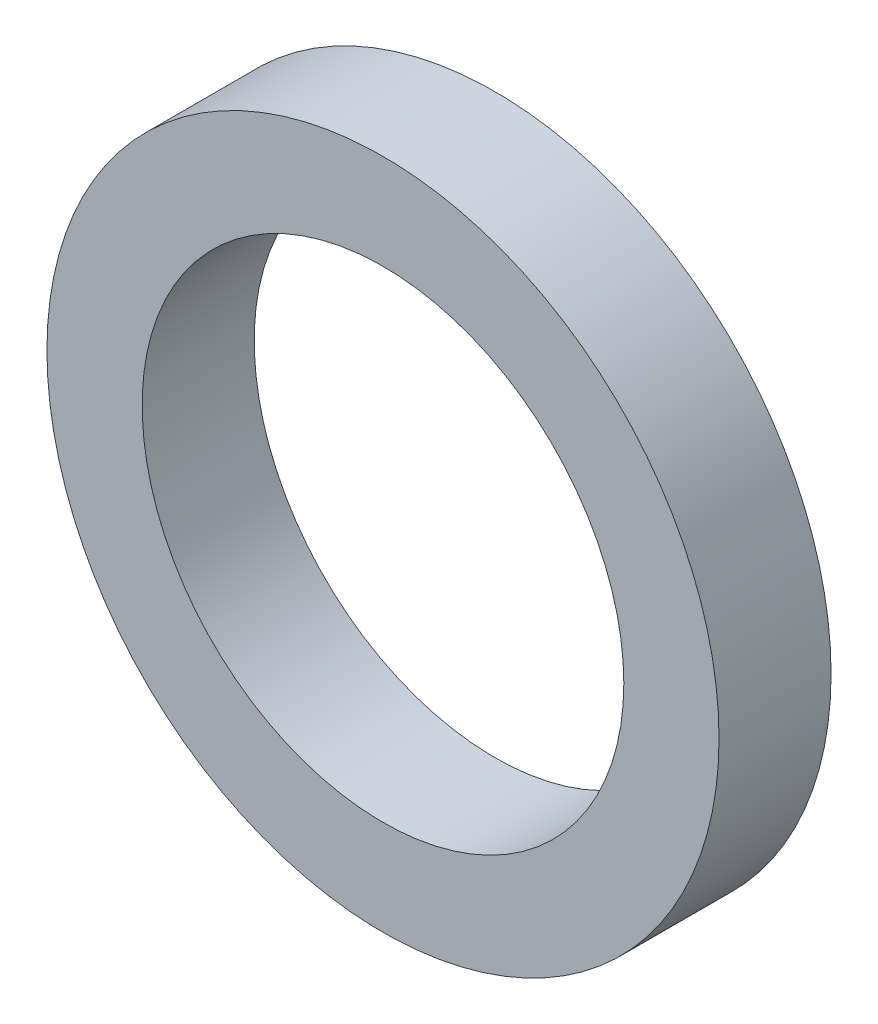
SolidWorks part; units mm, degrees
ref_plane "Front Plane" through (0, 0, 0) normal (0, 0, 1) x (1, 0, 0)
ref_plane "Top Plane" through (0, 0, 0) normal (0, 1, 0) x (1, 0, 0)
ref_plane "Right Plane" through (0, 0, 0) normal (1, 0, 0) x (0, 0, -1)
sketch "Sketch1" plane through (0, 0, 0) normal (0, 0, 1) x (1, 0, 0)
  circle A0 centre (0, 0) radius 2.15
  circle A1 centre (0, 0) radius 3
  dimension "D1" = 4.3
  dimension "D2" = 6
extrude "Boss-Extrude1" add sketch "Sketch1" along normal blind 1
